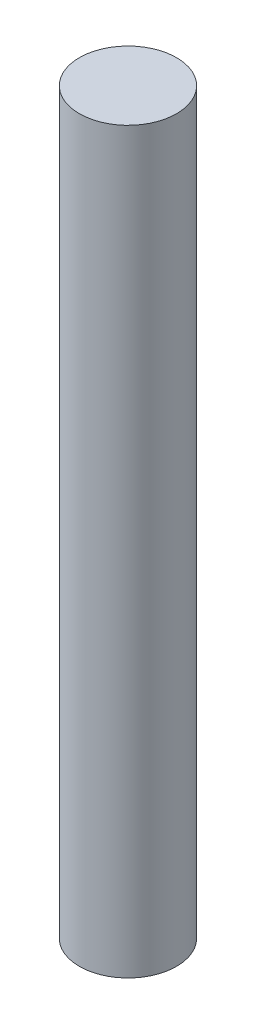
SolidWorks part; units mm, degrees
ref_plane "Front Plane" through (0, 0, 0) normal (0, 0, 1) x (1, 0, 0)
ref_plane "Top Plane" through (0, 0, 0) normal (0, 1, 0) x (1, 0, 0)
ref_plane "Right Plane" through (0, 0, 0) normal (1, 0, 0) x (0, 0, -1)
sketch "Sketch1" plane through (0, 0, 0) normal (0, 1, 0) x (1, 0, 0)
  circle A0 centre (0, 0) radius 2.5
  dimension "D1" = 5
extrude "Boss-Extrude1" add sketch "Sketch1" along normal blind 38 contours A0
